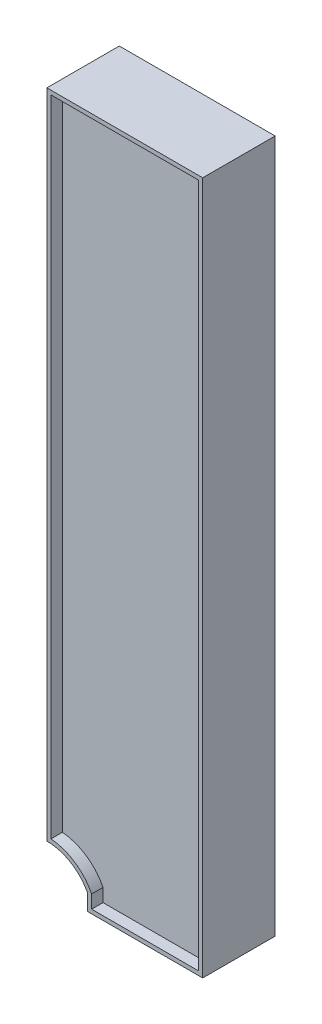
SolidWorks part; units mm, degrees
material "6061-T4 (SS)"
ref_plane "Front Plane" through (0, 0, 0) normal (0, 0, 1) x (1, 0, 0)
ref_plane "Top Plane" through (0, 0, 0) normal (0, 1, 0) x (1, 0, 0)
ref_plane "Right Plane" through (0, 0, 0) normal (1, 0, 0) x (0, 0, -1)
sketch "Sketch1" plane through (0, 0, 0) normal (0, 0, 1) x (1, 0, 0)
  line L1 (0, 0) -> (191.44, 0)
  line L2 (0, 0) -> (0, 851.41)
  line L3 (0, 851.41) -> (191.44, 851.41)
  line L4 (191.44, 0) -> (191.44, 851.41)
  dimension "D1" = 191.44
  dimension "D2" = 851.41
extrude "Boss-Extrude1" add sketch "Sketch1" along normal blind 89
ref_plane "Plane1" through (0, 0, 44.5) normal (0, 0, 1) x (1, 0, 0)
sketch "Sketch2" plane through (0, 0, 89) normal (0, 0, 1) x (1, 0, 0)
  line L0 (50, 0) -> (50, 20)
  line L1 (0, 0) -> (191.44, 0) construction
  line L2 (0, 851.41) -> (0, 0) construction
  line L3 (0, 50) -> (-42.5027, 50)
  line L4 (-42.5027, 50) -> (0, -54.7616)
  line L5 (0, -54.7616) -> (50, 0)
  arc A0 (50, 20) -> (0, 50) centre (0, -6.6667) ccw
  dimension "D1" = 20
  dimension "D2" = 50
  dimension "D3" = 50
extrude "Cut-Extrude1" cut sketch "Sketch2" against normal up to surface (89 mm away) contours L4 L5 L0 A0 L3 up to face at (95.72, 425.705, 0)
sketch "Sketch3" plane through (0, 0, 89) normal (0, 0, 1) x (1, 0, 0)
  line L15 (55, 21.222) -> (55, 5)
  line L16 (55, 5) -> (186.44, 5)
  line L17 (186.44, 5) -> (186.44, 846.41)
  line L18 (186.44, 846.41) -> (5, 846.41)
  line L19 (5, 846.41) -> (5, 54.797)
  line L20 (55, 21.222) -> (55, 5)
  line L21 (55, 5) -> (186.44, 5)
  line L22 (186.44, 5) -> (186.44, 846.41)
  line L23 (186.44, 846.41) -> (5, 846.41)
  line L24 (5, 846.41) -> (5, 54.797)
  arc A3 (55, 21.222) -> (5, 54.797) centre (0, -6.6667) ccw
  arc A4 (55, 21.222) -> (5, 54.797) centre (0, -6.6667) ccw
  dimension "D1" = 5
extrude "Cut-Extrude2" cut sketch "Sketch3" against normal blind 14
mirror "Mirror1" about plane through (0, 0, 44.5) normal (0, 0, 1) of "Cut-Extrude2"
